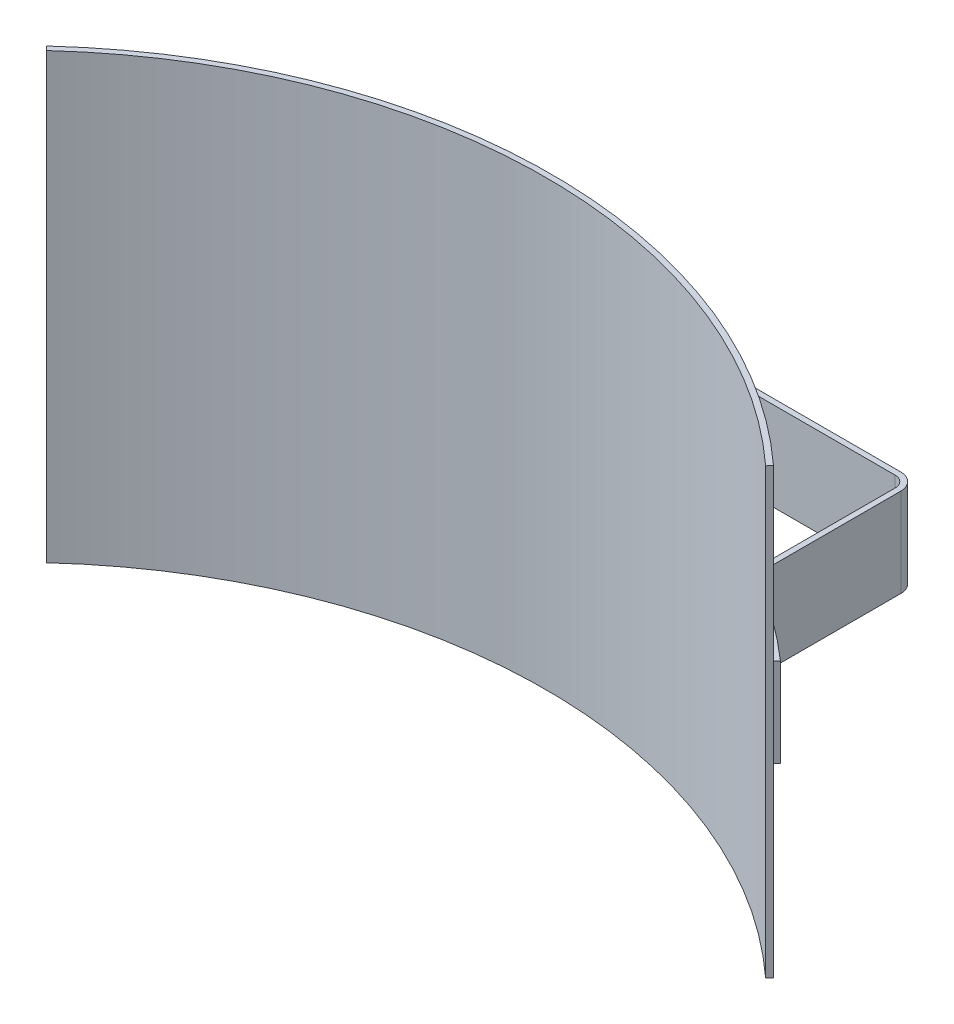
SolidWorks part; units mm, degrees
ref_plane "Front Plane" through (0, 0, 0) normal (0, 0, 1) x (1, 0, 0)
ref_plane "Top Plane" through (0, 0, 0) normal (0, 1, 0) x (1, 0, 0)
ref_plane "Right Plane" through (0, 0, 0) normal (1, 0, 0) x (0, 0, -1)
sketch "Sketch1" plane through (0, 0, 0) normal (0, 1, 0) x (1, 0, 0)
  line L0 (0, 0) -> (104.0324, 113.5315) construction
  line L1 (0, 0) -> (-104.0324, 113.5315) construction
  line L3 (0, 0) -> (0, 152.4) construction
  line L4 (104.0324, 113.5315) -> (102.9599, 112.3611)
  line L5 (-104.0324, 113.5315) -> (-102.9599, 112.3611)
  circle A0 centre (0, 0) radius 152.4 construction
  circle A1 centre (0, 0) radius 153.9875 construction
  arc A2 (102.9599, 112.3611) -> (-102.9599, 112.3611) centre (0, 0) ccw
  arc A3 (104.0324, 113.5315) -> (-104.0324, 113.5315) centre (0, 0) ccw
  dimension "D1" = 304.8
  dimension "D3" = 85
  dimension "D4" = 42.5
  dimension "D2" = 1.5875
extrude "Boss-Extrude1" add sketch "Sketch1" along normal mid plane 127
sketch "Sketch2" plane through (0, 0, 0) normal (0, 1, 0) x (1, 0, 0)
  line L0 (0, 153.9875) -> (0, 260.8018) construction
  line L1 (73.025, 179.3875) -> (-73.025, 179.3875)
  line L2 (-76.2, 176.2125) -> (-76.2, 135.6453)
  line L3 (76.2, 176.2125) -> (76.2, 135.6453)
  line L4 (77.7875, 176.2125) -> (77.7875, 135.6453)
  line L5 (73.025, 180.975) -> (-73.025, 180.975)
  line L6 (-77.7875, 176.2125) -> (-77.7875, 135.6453)
  line L7 (102.6474, 116.9063) -> (101.6, 115.7134)
  line L8 (-102.6474, 116.9063) -> (-101.6, 115.7134)
  arc A0 (104.0324, 113.5315) -> (-104.0324, 113.5315) centre (0, 0) ccw construction
  arc A1 (-77.7715, 132.905) -> (-101.6, 115.7134) centre (0, 0) ccw
  arc A2 (-76.2, 135.6453) -> (-77.7715, 132.905) centre (-79.375, 135.6453) cw
  arc A3 (-76.2, 176.2125) -> (-73.025, 179.3875) centre (-73.025, 176.2125) cw
  arc A4 (77.7715, 132.905) -> (101.6, 115.7134) centre (0, 0) cw
  arc A5 (76.2, 135.6453) -> (77.7715, 132.905) centre (79.375, 135.6453) ccw
  arc A6 (76.2, 176.2125) -> (73.025, 179.3875) centre (73.025, 176.2125) ccw
  arc A7 (78.5732, 134.2752) -> (102.6474, 116.9063) centre (0, 0) cw
  arc A8 (77.7875, 135.6453) -> (78.5732, 134.2752) centre (79.375, 135.6453) ccw
  arc A9 (77.7875, 176.2125) -> (73.025, 180.975) centre (73.025, 176.2125) ccw
  arc A10 (-77.7875, 176.2125) -> (-73.025, 180.975) centre (-73.025, 176.2125) cw
  arc A11 (-77.7875, 135.6453) -> (-78.5732, 134.2752) centre (-79.375, 135.6453) cw
  arc A12 (-78.5732, 134.2752) -> (-102.6474, 116.9063) centre (0, 0) ccw
  point P13 (-76.2, 133.8122)
  point P16 (-76.2, 179.3875)
  point P24 (76.2, 179.3875)
  point P25 (0, 179.3875)
  dimension "D3" = 25.4
  dimension "D4" = 3.175
  dimension "D1" = 76.2
  dimension "D2" = 25.4
  dimension "D5" = 1.5875
extrude "Boss-Extrude2" add sketch "Sketch2" along normal mid plane 25.4
equation "\"D4@Sketch1\"=\"D3@Sketch1\"/2"
